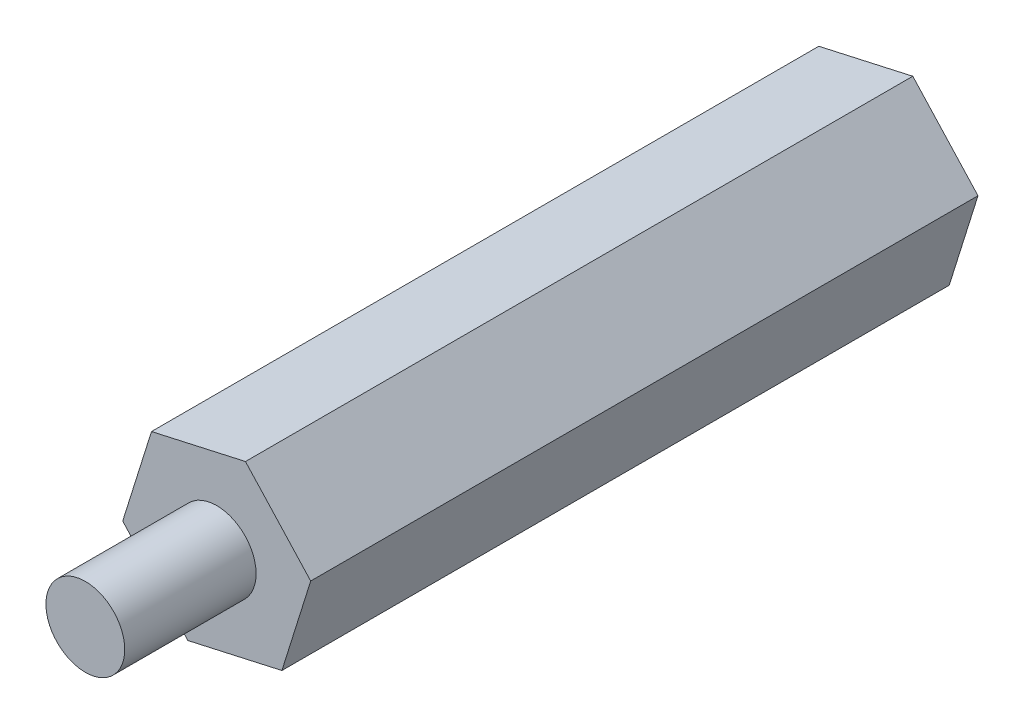
SolidWorks part; units mm, degrees
ref_plane "Front Plane" through (0, 0, 0) normal (0, 0, 1) x (1, 0, 0)
ref_plane "Top Plane" through (0, 0, 0) normal (0, 1, 0) x (1, 0, 0)
ref_plane "Right Plane" through (0, 0, 0) normal (1, 0, 0) x (0, 0, -1)
sketch "Sketch1" plane through (0, 0, 0) normal (0, 0, 1) x (1, 0, 0)
  line L1 (2.482, -2.6982) -> (3.5777, 0.8004)
  line L2 (3.5777, 0.8004) -> (1.0957, 3.4986)
  line L3 (1.0957, 3.4986) -> (-2.482, 2.6982)
  line L4 (-2.482, 2.6982) -> (-3.5777, -0.8004)
  line L5 (-3.5777, -0.8004) -> (-1.0957, -3.4986)
  line L6 (-1.0957, -3.4986) -> (2.482, -2.6982)
  circle A0 centre (0, 0) radius 3.175 construction
  circle A1 centre (0, 0) radius 1.5
  dimension "D1" = 3
  dimension "D2" = 6.35
extrude "Boss-Extrude1" add sketch "Sketch1" along normal blind 25.4
sketch "Sketch2" plane through (0, 0, 25.4) normal (0, 0, 1) x (1, 0, 0)
  circle A0 centre (0, 0) radius 1.5
  dimension "D1" = 3
extrude "Boss-Extrude2" add sketch "Sketch2" along normal blind 5
sketch "Sketch3" plane through (0, 0, 0) normal (0, 0, -1) x (-1, 0, 0)
  circle A0 centre (0, 0) radius 1.5
extrude "Boss-Extrude3" [suppressed] add sketch "Sketch3" along normal blind 5
